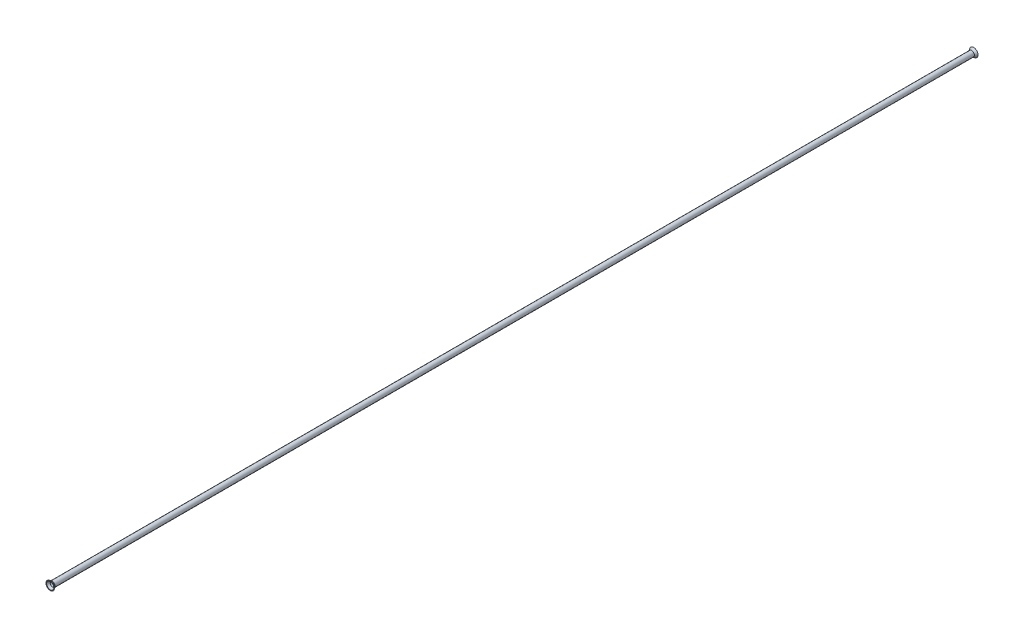
SolidWorks part; units mm, degrees
material "6061-T6 (SS)"
ref_plane "Front Plane" through (0, 0, 0) normal (0, 0, 1) x (1, 0, 0)
ref_plane "Top Plane" through (0, 0, 0) normal (0, 1, 0) x (1, 0, 0)
ref_plane "Right Plane" through (0, 0, 0) normal (1, 0, 0) x (0, 0, -1)
sketch "Sketch1" plane through (0, 0, 0) normal (0, 0, 1) x (1, 0, 0)
  circle A0 centre (0, 0) radius 2.3813
  circle A1 centre (0, 0) radius 1.8225
  dimension "D1" = 0.5588
  dimension "D2" = 4.7625
extrude "Boss-Extrude1" add sketch "Sketch1" along normal mid plane 798.1975
sketch "Sketch2" plane through (0, 0, 399.0988) normal (0, 0, 1) x (1, 0, 0)
  circle A0 centre (0, 0) radius 2.3813 construction
  circle A2 centre (0, 0) radius 2.3813
extrude "Boss-Extrude2" add sketch "Sketch2" along normal blind 1.778 draft 37 draft outward yes
sketch "Sketch3" plane through (0, 0, 399.0988) normal (0, 0, -1) x (-1, 0, 0)
  circle A0 centre (0, 0) radius 1.8225 construction
  circle A1 centre (0, 0) radius 1.8225
extrude "Cut-Extrude1" cut sketch "Sketch3" against normal through all draft 37 draft outward yes
mirror "Mirror1" about plane through (0, 0, 0) normal (0, 0, 1) of "Cut-Extrude1", "Boss-Extrude2"
